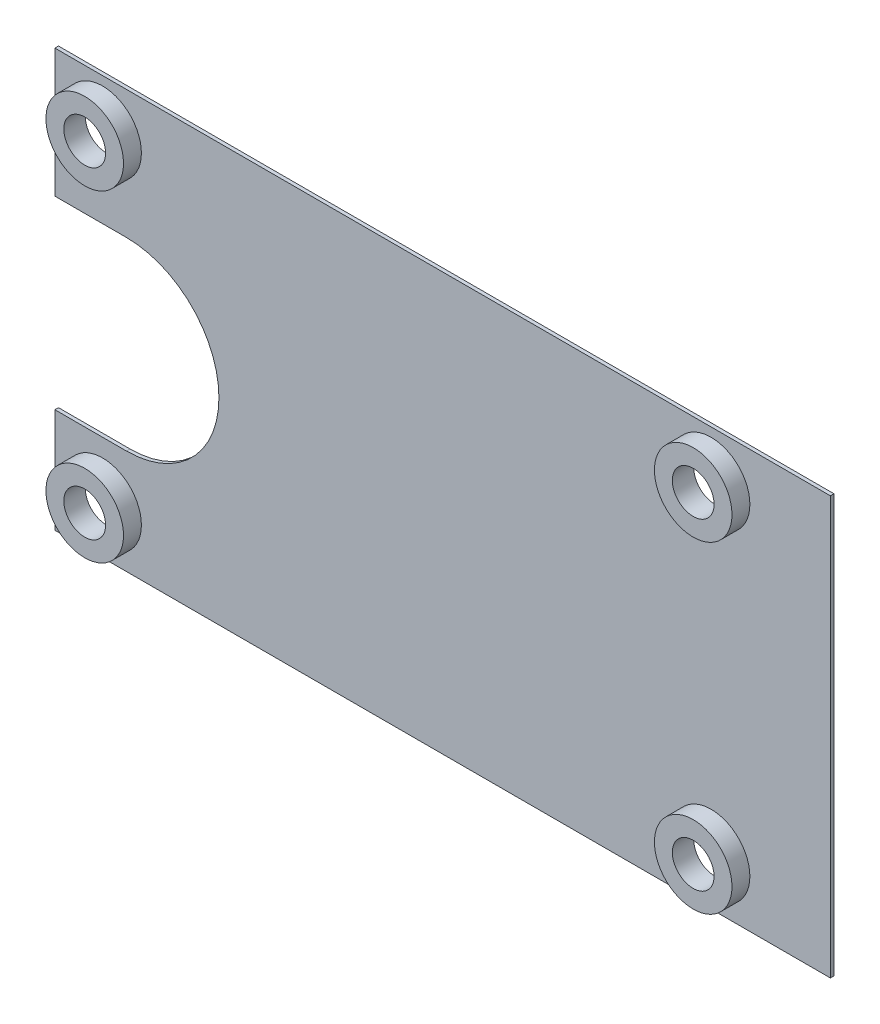
SolidWorks part; units mm, degrees
ref_plane "Front Plane" through (0, 0, 0) normal (0, 0, 1) x (1, 0, 0)
ref_plane "Top Plane" through (0, 0, 0) normal (0, 1, 0) x (1, 0, 0)
ref_plane "Right Plane" through (0, 0, 0) normal (1, 0, 0) x (0, 0, -1)
sketch "Sketch2" plane through (0, 0, 0) normal (0, 0, 1) x (1, 0, 0)
  line L1 (-32.5, 17.5) -> (32.5, 17.5)
  line L2 (-32.5, 17.5) -> (-32.5, -17.5)
  line L3 (-32.5, -17.5) -> (32.5, -17.5)
  line L4 (32.5, 17.5) -> (32.5, -17.5)
  line L5 (-32.5, 17.5) -> (32.5, -17.5) construction
  line L6 (-32.5, -17.5) -> (32.5, 17.5) construction
  point P0 (0, 0)
  dimension "D1" = 65
  dimension "D2" = 35
extrude "Boss-Extrude1" add sketch "Sketch2" along normal blind 0.3
sketch "Sketch3" plane through (0, 0, 0.3) normal (0, 0, 1) x (1, 0, 0)
  line L0 (-32.5, -17.5) -> (32.5, -17.5) construction
  line L1 (-28.5, 13.5) -> (22.5, 13.5) construction
  line L2 (-28.5, 13.5) -> (-28.5, -13.5) construction
  line L3 (-28.5, -13.5) -> (22.5, -13.5) construction
  line L4 (22.5, 13.5) -> (22.5, -13.5) construction
  line L5 (-32.5, 17.5) -> (-32.5, -17.5) construction
  circle A0 centre (-28.5, 13.5) radius 1.75
  circle A1 centre (-28.5, -13.5) radius 1.75
  circle A2 centre (22.5, 13.5) radius 1.75
  circle A3 centre (22.5, -13.5) radius 1.75
  dimension "D1" = 3.5
  dimension "D2" = 4
  dimension "D3" = 4
  dimension "D4" = 31
  dimension "D5" = 55
extrude "Cut-Extrude1" cut sketch "Sketch3" against normal blind 1.6
sketch "Sketch4" plane through (0, 0, 0.3) normal (0, 0, 1) x (1, 0, 0)
  circle A0 centre (-28.5, -13.5) radius 1.75 construction
  circle A1 centre (22.5, -13.5) radius 1.75 construction
  circle A2 centre (22.5, 13.5) radius 1.75 construction
  circle A3 centre (-28.5, 13.5) radius 1.75 construction
  circle A4 centre (-28.5, -13.5) radius 1.75
  circle A5 centre (22.5, -13.5) radius 1.75
  circle A6 centre (22.5, 13.5) radius 1.75
  circle A7 centre (-28.5, 13.5) radius 1.75
  circle A8 centre (-28.5, 13.5) radius 3.25
  circle A9 centre (-28.5, -13.5) radius 3.25
  circle A10 centre (22.5, -13.5) radius 3.25
  circle A11 centre (22.5, 13.5) radius 3.25
  dimension "D1" = 6.5
extrude "Boss-Extrude2" add sketch "Sketch4" along normal blind 1.5
sketch "Sketch5" plane through (0, 0, 0.3) normal (0, 0, 1) x (1, 0, 0)
  line L0 (-32.5, -1) -> (-26.5, -1) construction
  line L5 (-32.5, 17.5) -> (-32.5, -17.5) construction
  line L6 (32.5, 17.5) -> (-32.5, 17.5) construction
  line L7 (-32.5, 6.75) -> (-26.5, 6.75)
  line L8 (-32.5, -8.75) -> (-26.5, -8.75)
  arc A0 (-32.5, 6.75) -> (-32.5, -8.75) centre (-32.5, -1) ccw
  arc A1 (-26.5, -8.75) -> (-26.5, 6.75) centre (-26.5, -1) ccw
  point P0 (-26.5, -0.5238)
  point P7 (-29.5, -1)
  dimension "D1" = 15.5
  dimension "D2" = 6
  dimension "D3" = 18.5
extrude "Cut-Extrude2" cut sketch "Sketch5" against normal blind 10
